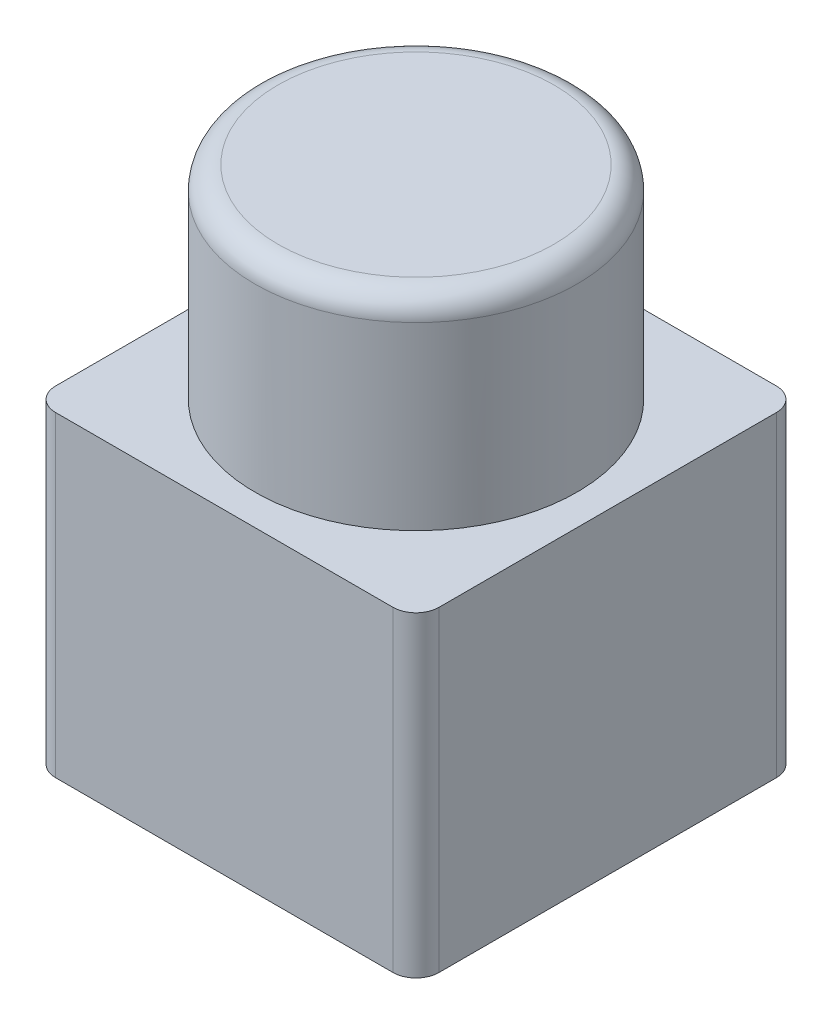
SolidWorks part; units mm, degrees
ref_plane "Front Plane" through (0, 0, 0) normal (0, 0, 1) x (1, 0, 0)
ref_plane "Top Plane" through (0, 0, 0) normal (0, 1, 0) x (1, 0, 0)
ref_plane "Right Plane" through (0, 0, 0) normal (1, 0, 0) x (0, 0, -1)
sketch "Sketch1" plane through (0, 0, 0) normal (0, 1, 0) x (1, 0, 0)
  line L1 (0, 0) -> (50, 0)
  line L2 (0, 0) -> (0, 50)
  line L3 (0, 50) -> (50, 50)
  line L4 (50, 0) -> (50, 50)
  dimension "D1" = 50
extrude "Boss-Extrude1" add sketch "Sketch1" along normal blind 41.25 contours L3 L4 L1 L2
sketch "Sketch2" plane through (0, 0, 0) normal (0, -1, 0) x (1, 0, 0)
  line L0 (5, -5) -> (45, -45) construction
  line L1 (25, 0) -> (25, -25) construction
  line L2 (0, 0) -> (50, 0) construction
  line L3 (25, -25) -> (25, -50) construction
  line L4 (0, -50) -> (50, -50) construction
  line L5 (5, -5) -> (5, 0) construction
  line L6 (5, -5) -> (0, -5) construction
  line L7 (0, 0) -> (0, -50) construction
  circle A0 centre (5, -5) radius 1.5
  circle A1 centre (45, -45) radius 1.5
  dimension "D3" = 3
  dimension "D1" = 40
  dimension "D2" = 40
extrude "Cut-Extrude1" cut sketch "Sketch2" against normal blind 6 contours A1 | A0
sketch "Sketch3" plane through (0, 41.25, 0) normal (0, 1, 0) x (1, 0, 0)
  line L0 (25, 50) -> (25, 25) construction
  line L1 (0, 50) -> (50, 50) construction
  line L2 (25, 25) -> (25, 0) construction
  line L3 (0, 0) -> (50, 0) construction
  line L4 (0, 25) -> (25, 25) construction
  line L5 (0, 0) -> (0, 50) construction
  line L6 (25, 25) -> (50, 25) construction
  line L7 (50, 0) -> (50, 50) construction
  circle A0 centre (25, 25) radius 21
  dimension "D1" = 42
extrude "Boss-Extrude2" add sketch "Sketch3" along normal blind 26.5
fillet "Fillet1" radius 3 5 edges at (25, 67.75, -4) (50, 20.625, -50) (0, 20.625, -50) (50, 20.625, 0) (0, 20.625, 0)
